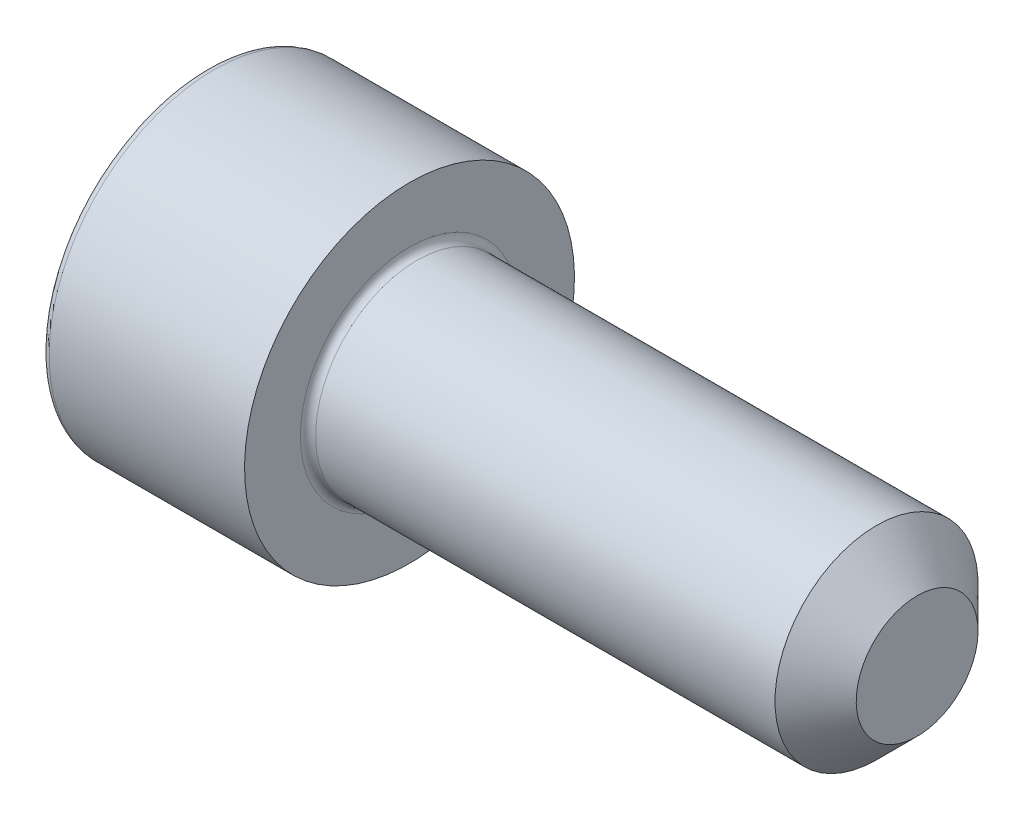
SolidWorks part; units mm, degrees
ref_plane "Спереди" through (0, 0, 0) normal (0, 0, 1) x (1, 0, 0)
ref_plane "Сверху" through (0, 0, 0) normal (0, 1, 0) x (1, 0, 0)
ref_plane "Справа" through (0, 0, 0) normal (1, 0, 0) x (0, 0, -1)
sketch "Эскиз1" plane through (0, 0, 0) normal (0, 0, 1) x (1, 0, 0)
  line L0 (0, 0) -> (0, 6.5)
  line L1 (0, 6.5) -> (8, 6.5)
  line L2 (8, 6.5) -> (8, 4)
  line L3 (8, 4) -> (28, 4)
  line L4 (28, 4) -> (28, 0)
  line L5 (28, 0) -> (0, 0) construction
  line L6 (0, 0) -> (28, 0)
  dimension "D1" = 13
  dimension "D2" = 8
  dimension "D3" = 8
  dimension "D4" = 20
revolve "Повернуть1" add sketch "Эскиз1" angle 360 about L5
cosmetic thread "Условное изображение резьбы1" parameters "D2"=6.619
sketch "Эскиз2" plane through (0, 0, 0) normal (-1, 0, 0) x (0, 0, 1)
  line L1 (-1.7321, 3) -> (-3.4641, 0)
  line L2 (-3.4641, 0) -> (-1.7321, -3)
  line L3 (-1.7321, -3) -> (1.7321, -3)
  line L4 (1.7321, -3) -> (3.4641, 0)
  line L5 (3.4641, 0) -> (1.7321, 3)
  line L6 (1.7321, 3) -> (-1.7321, 3)
  circle A0 centre (0, 0) radius 3 construction
  dimension "D1" = 6
extrude "Вырез-Вытянуть1" cut sketch "Эскиз2" against normal blind 2.5
fillet "Скругление1" radius 0.3 2 edges at (0, 6.5, 0) (8, 4, 0)
chamfer "Фаска1" distance 1.6 angle 45 1 edges at (28, 4, 0)
